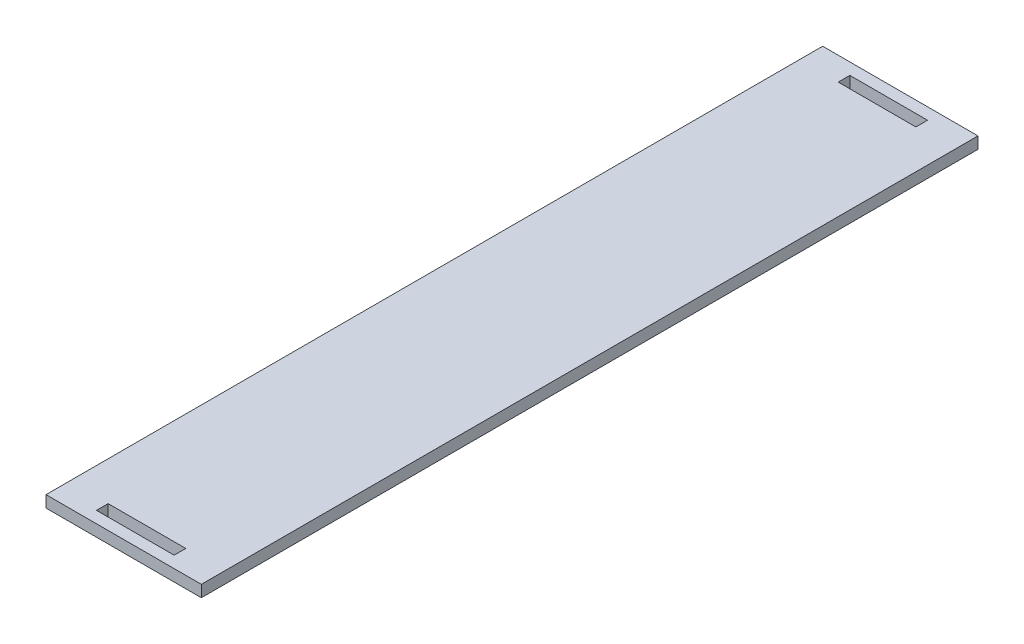
SolidWorks part; units mm, degrees
ref_plane "Plan de face" through (0, 0, 0) normal (0, 0, 1) x (1, 0, 0)
ref_plane "Plan de dessus" through (0, 0, 0) normal (0, 1, 0) x (1, 0, 0)
ref_plane "Plan de droite" through (0, 0, 0) normal (1, 0, 0) x (0, 0, -1)
sketch "Esquisse1" plane through (0, 0, 0) normal (0, 1, 0) x (1, 0, 0)
  line L0 (0, 100) -> (0, -100) construction
  line L1 (20, 100) -> (-20, 100)
  line L2 (20, 100) -> (20, -100)
  line L3 (20, -100) -> (-20, -100)
  line L4 (-20, 100) -> (-20, -100)
  line L5 (20, 100) -> (-20, -100) construction
  line L6 (20, -100) -> (-20, 100) construction
  line L7 (0, 0) -> (-20, 0) construction
  line L8 (10, -94) -> (-10, -94)
  line L9 (10, -94) -> (10, -97)
  line L10 (10, -97) -> (-10, -97)
  line L11 (-10, -94) -> (-10, -97)
  line L12 (10, -94) -> (-10, -97) construction
  line L13 (10, -97) -> (-10, -94) construction
  line L18 (10, 97) -> (-10, 97)
  line L19 (-10, 94) -> (-10, 97)
  line L20 (10, 94) -> (-10, 94)
  line L21 (10, 94) -> (10, 97)
  point P0 (0, 0)
  point P5 (0, -95.5)
  point P9 (0, 0)
  dimension "D1" = 40
  dimension "D2" = 200
  dimension "D3" = 20
  dimension "D4" = 3
  dimension "D5" = 3
extrude "Boss.-Extru.1" add sketch "Esquisse1" along normal blind 3
